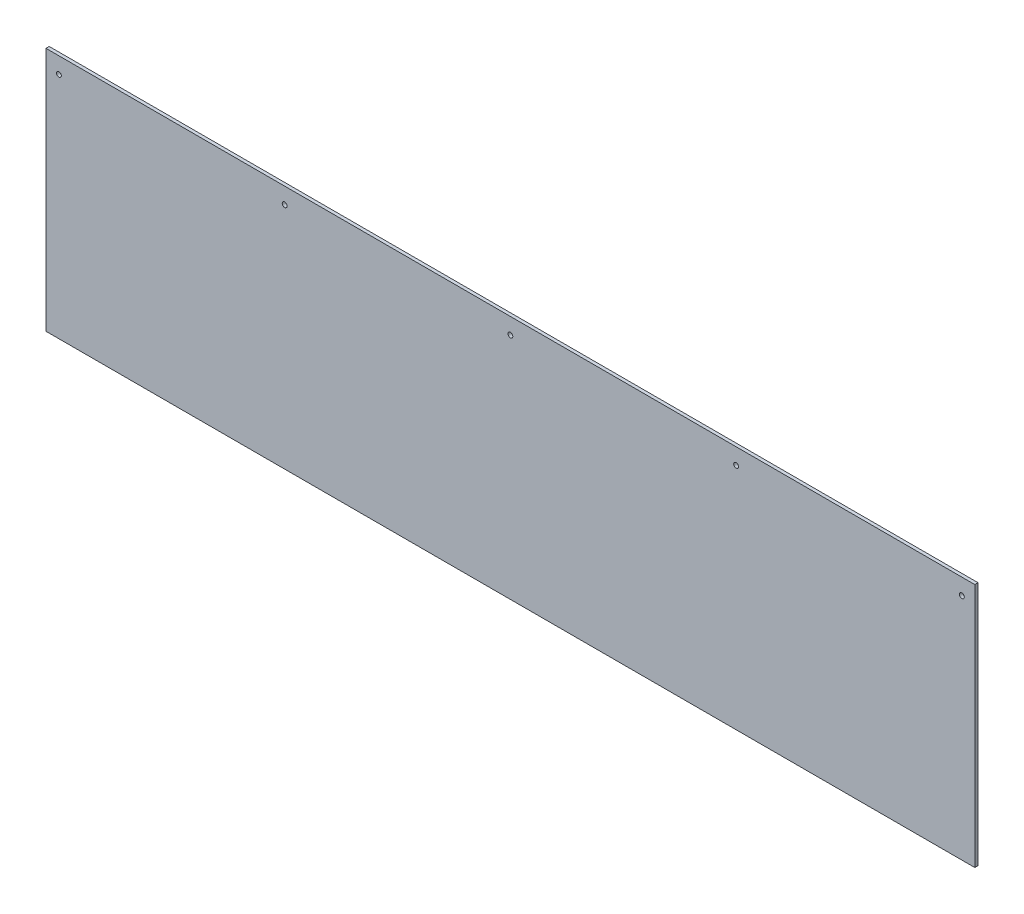
SolidWorks part; units mm, degrees
material "PC High Viscosity"
ref_plane "Front Plane" through (0, 0, 0) normal (0, 0, 1) x (1, 0, 0)
ref_plane "Top Plane" through (0, 0, 0) normal (0, 1, 0) x (1, 0, 0)
ref_plane "Right Plane" through (0, 0, 0) normal (1, 0, 0) x (0, 0, -1)
sketch "Sketch1" plane through (0, 0, 0) normal (0, 0, 1) x (1, 0, 0)
  line L1 (0, 0) -> (1828.8, 0)
  line L2 (0, 0) -> (0, 482.6)
  line L3 (0, 482.6) -> (1828.8, 482.6)
  line L4 (1828.8, 0) -> (1828.8, 482.6)
  dimension "D1" = 482.6
  dimension "D2" = 1828.8
extrude "Boss-Extrude1" add sketch "Sketch1" along normal blind 6.35
sketch "Sketch2" plane through (0, 0, 6.35) normal (0, 0, 1) x (1, 0, 0)
  line L0 (1828.8, 482.6) -> (0, 482.6) construction
  line L1 (0, 482.6) -> (0, 0) construction
  circle A0 centre (25.4, 450.85) radius 4.7625
  circle A1 centre (469.9, 450.85) radius 4.7625
  circle A2 centre (914.4, 450.85) radius 4.7625
  circle A3 centre (1358.9, 450.85) radius 4.7625
  circle A4 centre (1803.4, 450.85) radius 4.7625
  dimension "D1" = 9.525
  dimension "D4" = 469.9
  dimension "D5" = 914.4
  dimension "D6" = 1358.9
  dimension "D2" = 31.75
  dimension "D3" = 25.4
  dimension "D8" = 1803.4
extrude "Cut-Extrude1" cut sketch "Sketch2" against normal through all
